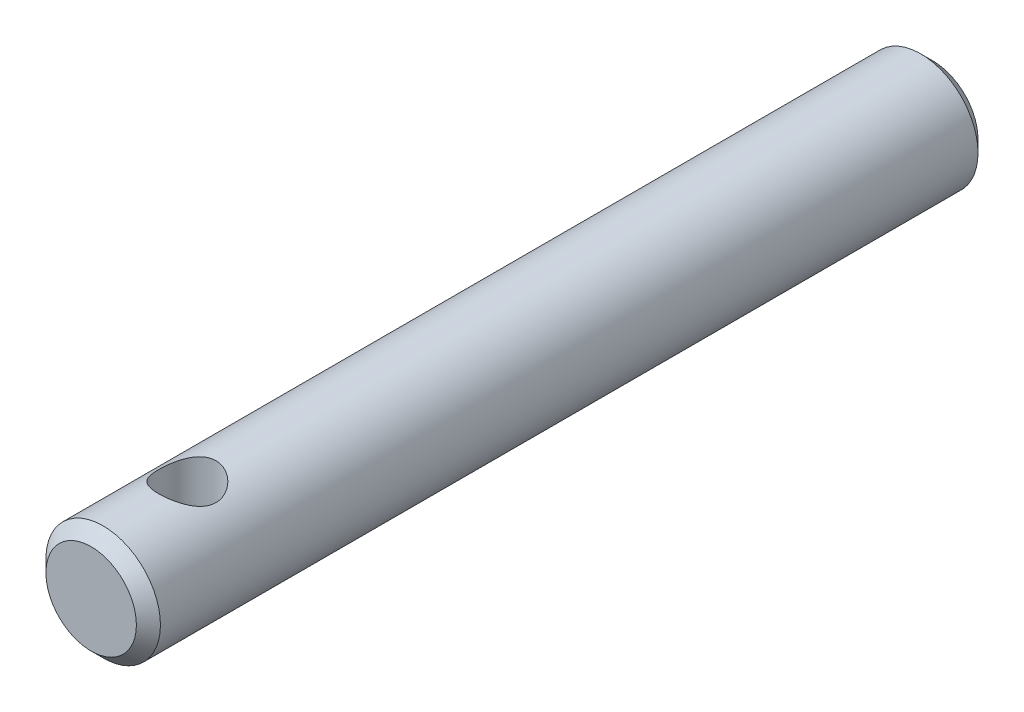
SolidWorks part; units mm, degrees
ref_plane "Front Plane" through (0, 0, 0) normal (0, 0, 1) x (1, 0, 0)
ref_plane "Top Plane" through (0, 0, 0) normal (0, 1, 0) x (1, 0, 0)
ref_plane "Right Plane" through (0, 0, 0) normal (1, 0, 0) x (0, 0, -1)
sketch "Sketch1" plane through (0, 0, 0) normal (0, 0, 1) x (1, 0, 0)
  circle A0 centre (0, 0) radius 2.3813
  dimension "D1" = 4.7625
extrude "Boss-Extrude1" add sketch "Sketch1" along normal mid plane 35
sketch "Sketch2" plane through (0, 0, 0) normal (0, 1, 0) x (1, 0, 0)
  line L0 (0, -17.5) -> (0, 17.5) construction
  line L1 (-2.3813, -17.5) -> (2.3813, -17.5) construction
  line L2 (2.3813, 17.5) -> (-2.3813, 17.5) construction
  circle A0 centre (0, -13.5) radius 1.1906
  dimension "D2" = 2.3813
  dimension "D1" = 4
extrude "Cut-Extrude2" cut sketch "Sketch2" against normal through all both and the other way through all
chamfer "Chamfer1" distance 0.5 angle 45 2 edges at (2.3813, 0, -17.5) (2.3813, 0, 17.5)
